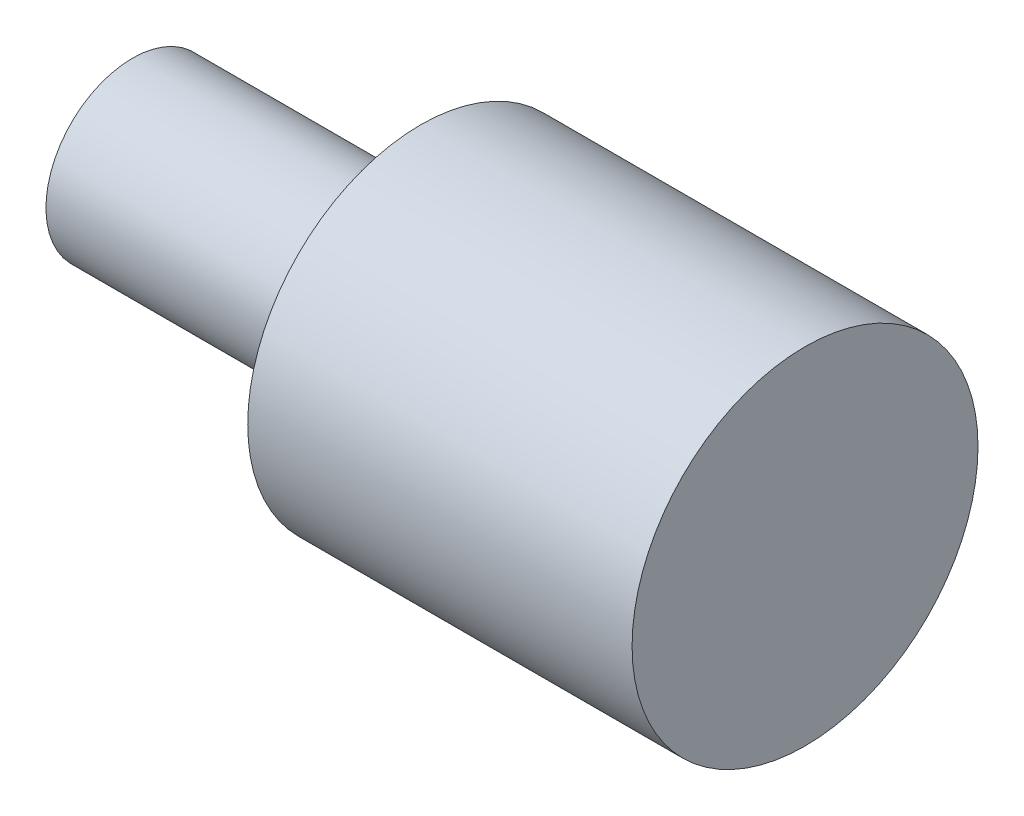
SolidWorks part; units mm, degrees
ref_plane "Спереди" through (0, 0, 0) normal (0, 0, 1) x (1, 0, 0)
ref_plane "Сверху" through (0, 0, 0) normal (0, 1, 0) x (1, 0, 0)
ref_plane "Справа" through (0, 0, 0) normal (1, 0, 0) x (0, 0, -1)
sketch "Эскиз1" plane through (0, 0, 0) normal (0, 0, 1) x (1, 0, 0)
  line L0 (0, 0) -> (0, 0.9)
  line L1 (0, 0.9) -> (3, 0.9)
  line L2 (3, 0.9) -> (3, 1.8)
  line L3 (3, 1.8) -> (7, 1.8)
  line L4 (7, 1.8) -> (7, 0)
  line L5 (7, 0) -> (0, 0)
  line L6 (-0.7526, 0) -> (0, 0) construction
  dimension "D1" = 1.8
  dimension "D2" = 3.6
  dimension "D3" = 7
  dimension "D4" = 3
revolve "Повернуть1" add sketch "Эскиз1" angle 360 about L5
